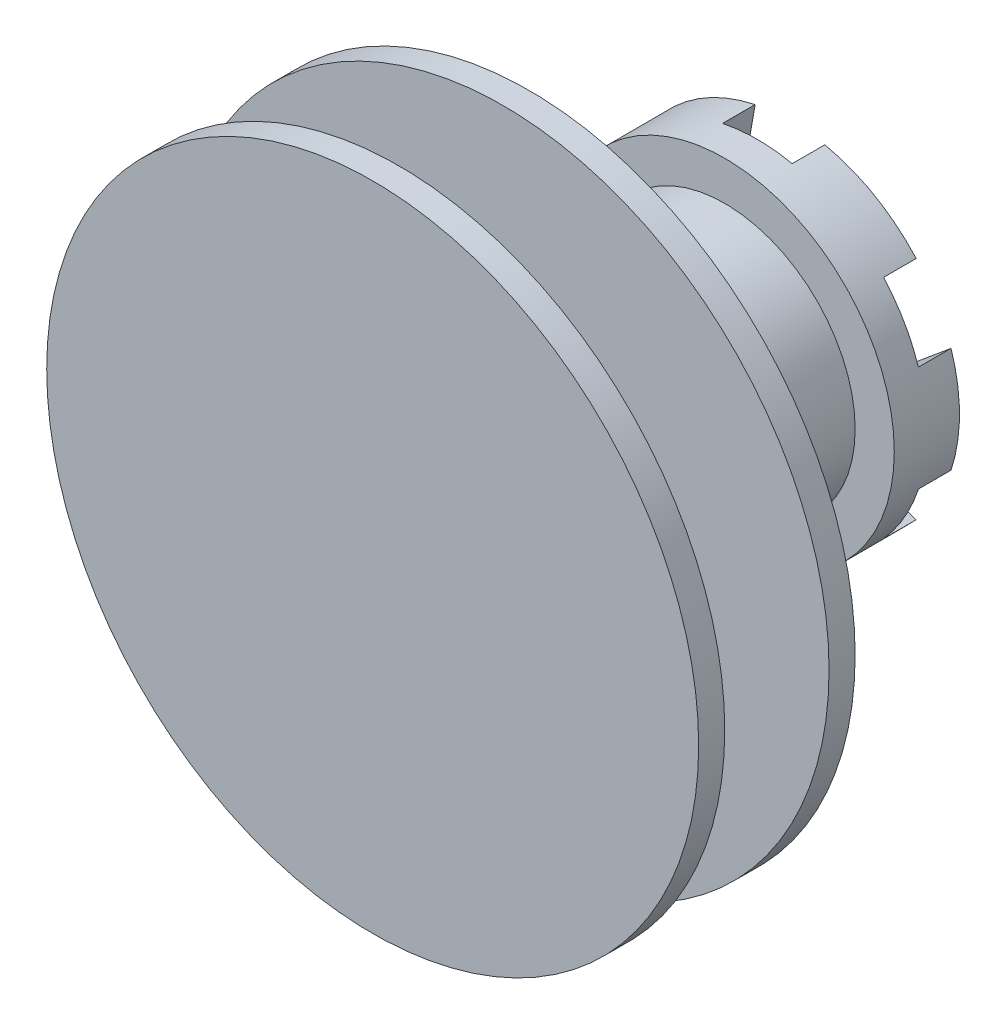
SolidWorks part; units mm, degrees
ref_plane "正面(Front)" through (0, 0, 0) normal (0, 0, 1) x (1, 0, 0)
ref_plane "平面(Top)" through (0, 0, 0) normal (0, 1, 0) x (1, 0, 0)
ref_plane "右側面(Right)" through (0, 0, 0) normal (1, 0, 0) x (0, 0, -1)
sketch "ｽｹｯﾁ1" plane through (0, 0, 0) normal (0, 0, 1) x (1, 0, 0)
  line L0 (0, 0) -> (0, 32.0386) construction
  line L1 (3.75, 6.4952) -> (2.4634, 13.9265)
  line L2 (0, 0) -> (3.75, 6.4952) construction
  arc A0 (2.4634, 13.9265) -> (0, 16) centre (0, 13.5) ccw
  dimension "D1" = 2.5
  dimension "D2" = 7.5
  dimension "D3" = 30
  dimension "D4" = 16
sketch "ｽｹｯﾁ2" plane through (0, 0, 0) normal (0, 0, 1) x (1, 0, 0)
  line L0 (3.75, 6.4952) -> (2.4634, 13.9265) construction
  line L1 (3.75, 6.4952) -> (2.4634, 13.9265)
  line L3 (0, 0) -> (0, 32.0386) construction
  line L4 (0, 0) -> (0, 32.0386) construction
  line L5 (-3.75, 6.4952) -> (-2.4634, 13.9265)
  line L6 (7.5, 0) -> (13.2924, 4.8299)
  line L7 (3.75, 6.4952) -> (10.829, 9.0966)
  line L8 (3.75, -6.4952) -> (10.829, -9.0966)
  line L9 (7.5, 0) -> (13.2924, -4.8299)
  line L10 (-3.75, -6.4952) -> (-2.4634, -13.9265)
  line L11 (3.75, -6.4952) -> (2.4634, -13.9265)
  line L12 (-7.5, 0) -> (-13.2924, -4.8299)
  line L13 (-3.75, -6.4952) -> (-10.829, -9.0966)
  line L14 (-3.75, 6.4952) -> (-10.829, 9.0966)
  line L15 (-7.5, 0) -> (-13.2924, 4.8299)
  line L16 (0, 0) -> (3.75, 6.4952) construction
  arc A0 (2.4634, 13.9265) -> (0, 16) centre (0, 13.5) ccw construction
  arc A1 (2.4634, 13.9265) -> (-2.4634, 13.9265) centre (0, 13.5) ccw
  arc A2 (13.2924, 4.8299) -> (10.829, 9.0966) centre (11.6913, 6.75) ccw
  arc A3 (10.829, -9.0966) -> (13.2924, -4.8299) centre (11.6913, -6.75) ccw
  arc A4 (-2.4634, -13.9265) -> (2.4634, -13.9265) centre (0, -13.5) ccw
  arc A5 (-13.2924, -4.8299) -> (-10.829, -9.0966) centre (-11.6913, -6.75) ccw
  arc A6 (-10.829, 9.0966) -> (-13.2924, 4.8299) centre (-11.6913, 6.75) ccw
  dimension "D2" = 7.5
  dimension "D3" = 30
  dimension "D1" = 6
sketch "ｽｹｯﾁ3" plane through (0, 0, 0) normal (0, 0, 1) x (1, 0, 0)
  circle A0 centre (0, 0) radius 13
  dimension "D1" = 26
extrude "ﾎﾞｽ - 押し出し1" add sketch "ｽｹｯﾁ3" along normal blind 5
extrude "ｶｯﾄ - 押し出し2" cut sketch "ｽｹｯﾁ2" along normal blind 2.5
sketch "ｽｹｯﾁ4" plane through (0, 0, 5) normal (0, 0, 1) x (1, 0, 0)
  circle A0 centre (0, 0) radius 10
  dimension "D1" = 20
extrude "ﾎﾞｽ - 押し出し2" add sketch "ｽｹｯﾁ4" along normal blind 15
sketch "ｽｹｯﾁ5" plane through (0, 0, 0) normal (0, 1, 0) x (1, 0, 0)
  line L0 (0, 0) -> (0, -21.9976) construction
  line L1 (0, -20) -> (25, -20)
  line L2 (-10, -20) -> (10, -20) construction
  line L3 (25, -20) -> (25, -22)
  line L4 (25, -22) -> (10, -22)
  line L5 (10, -22) -> (10, -30)
  line L6 (10, -30) -> (25, -30)
  line L7 (25, -30) -> (25, -32)
  line L8 (25, -32) -> (0, -32)
  line L9 (0, -20) -> (0, -32)
  dimension "D1" = 2
  dimension "D2" = 2
  dimension "D3" = 8
  dimension "D4" = 10
  dimension "D5" = 25
revolve "回転1" add sketch "ｽｹｯﾁ5" angle 360 about L0
